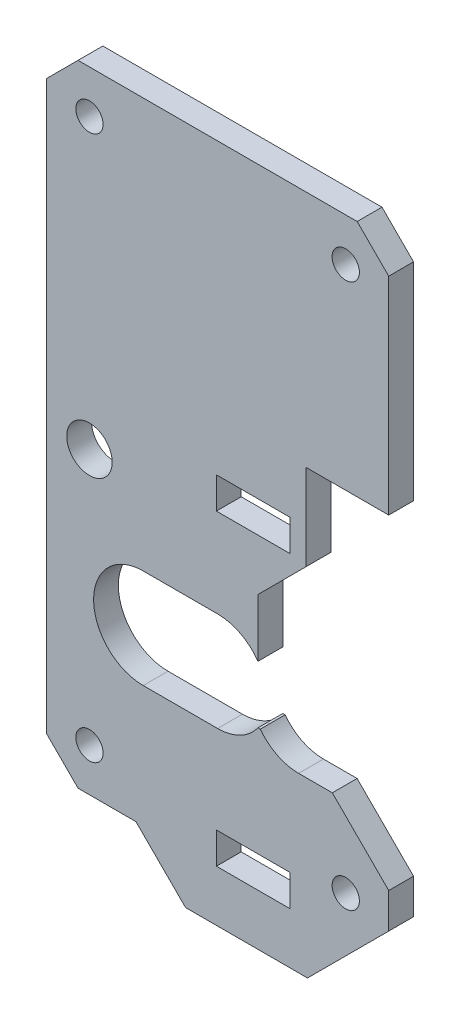
SolidWorks part; units mm, degrees
ref_plane "Front Plane" through (0, 0, 0) normal (0, 0, 1) x (1, 0, 0)
ref_plane "Top Plane" through (0, 0, 0) normal (0, 1, 0) x (1, 0, 0)
ref_plane "Right Plane" through (0, 0, 0) normal (1, 0, 0) x (0, 0, -1)
sketch "Sketch1" plane through (0, 0, 0) normal (0, 0, 1) x (1, 0, 0)
  line L0 (5.1665, -3.482) -> (4.8863, -3.482) construction
  line L1 (13.8757, -5.8) -> (9.805, -5.8) construction
  line L2 (20.7, 26.7) -> (20.7, 51.7327)
  line L3 (20.7, 26.7) -> (10.7, 26.7)
  line L4 (10.7, 26.7) -> (10.7, 16.2957)
  line L5 (10.7, 16.2957) -> (4.8863, 10.482)
  line L6 (4.8863, 10.482) -> (4.8863, 3.482)
  line L7 (20.7, -12.6243) -> (13.8757, -5.8) construction
  line L8 (20.7, -16.8757) -> (20.7, -12.6243) construction
  line L9 (10.8757, -26.7) -> (20.7, -16.8757) construction
  line L10 (2.5729, 20.5) -> (6.0371, 20.5)
  line L11 (2.5729, 55.55) -> (6.0371, 55.55)
  line L12 (2.5729, -20.5) -> (6.0371, -20.5)
  line L13 (6.0371, -26.7) -> (2.5729, -26.7)
  line L14 (5.1665, -3.482) -> (4.8863, -3.482)
  line L15 (13.8757, -5.8) -> (9.805, -5.8)
  line L16 (20.7, -12.6243) -> (13.8757, -5.8)
  line L17 (20.7, -16.8757) -> (20.7, -12.6243)
  line L18 (10.8757, -26.7) -> (20.7, -16.8757)
  line L84 (20.7, 51.7327) -> (16.8827, 55.55)
  line L85 (16.8827, 55.55) -> (6.0371, 55.55)
  line L87 (6.0371, 20.5) -> (8.755, 20.5)
  line L88 (8.755, 20.5) -> (8.755, 16.7)
  line L89 (8.755, 16.7) -> (-0.145, 16.7)
  line L90 (-0.145, 16.7) -> (-0.145, 20.5)
  line L91 (-0.145, 20.5) -> (2.5729, 20.5)
  line L93 (2.5729, 55.55) -> (-16.8827, 55.55)
  line L94 (-16.8827, 55.55) -> (-20.7, 51.7327)
  line L95 (-20.7, 51.7327) -> (-20.7, 16.8757)
  line L96 (-20.7, 16.8757) -> (-20.7, -16.8757)
  line L97 (-20.7, -16.8757) -> (-16.8757, -20.7)
  line L98 (-16.8757, -20.7) -> (-9.8757, -20.7)
  line L99 (-9.8757, -20.7) -> (-3.8757, -26.7)
  line L100 (-3.8757, -26.7) -> (2.5729, -26.7)
  line L102 (2.5729, -20.5) -> (-0.145, -20.5)
  line L103 (-0.145, -20.5) -> (-0.145, -16.7)
  line L104 (-0.145, -16.7) -> (8.755, -16.7)
  line L105 (8.755, -16.7) -> (8.755, -20.5)
  line L106 (8.755, -20.5) -> (6.0371, -20.5)
  line L108 (6.0371, -26.7) -> (10.8757, -26.7)
  line L114 (0, -6) -> (-9, -6)
  line L115 (-9, 6) -> (0, 6)
  line L120 (20.7, 18.1132) -> (12.7, 18.1132)
  arc A0 (5.1665, -3.482) -> (9.805, -5.8) centre (9.805, 0) ccw construction
  circle A1 centre (-15.5, -15.5) radius 1.65
  arc A2 (5.1665, -3.482) -> (9.805, -5.8) centre (9.805, 0) ccw
  circle A3 centre (15.5, -15.5) radius 1.65 construction
  arc A4 (0, -6) -> (4.8863, -3.482) centre (0, 0) ccw
  circle A5 centre (15.5, -15.5) radius 1.65
  arc A12 (-9, 6) -> (-9, -6) centre (-9, 0) ccw
  arc A13 (4.8863, 3.482) -> (0, 6) centre (0, 0) ccw
  circle A14 centre (-15.5, 15.5) radius 2.75
  circle A16 centre (-15.5, 50.35) radius 1.65
  circle A18 centre (15.5, 50.35) radius 1.65
  dimension "D7" = 3.3
  dimension "D1" = 5.5
  dimension "D8" = 3.3
  dimension "D9" = 3.3
  dimension "D10" = 6
  dimension "D11" = 6
  dimension "D12" = 6
  dimension "D2" = 135
  dimension "D3" = 10
  dimension "D4" = 7
  dimension "D13" = 2.5729
  dimension "D14" = 2.5729
  dimension "D16" = 4.8863
  dimension "D17" = 6.0371
  dimension "D18" = 6.0371
  dimension "D19" = 8.755
  dimension "D20" = 8.755
  dimension "D21" = 10.7
  dimension "D22" = 10.8757
  dimension "D23" = 12.7
  dimension "D24" = 15.5
  dimension "D25" = 16.8827
  dimension "D26" = 3.8757
  dimension "D27" = 9.8757
  dimension "D28" = 16.8757
  dimension "D29" = 16.8827
  dimension "D30" = 3.482
  dimension "D31" = 0.145
  dimension "D32" = 0.145
  dimension "D33" = 15.5
  dimension "D34" = 16.8757
  dimension "D35" = 9
  dimension "D36" = 9
  dimension "D37" = 26.7
  dimension "D38" = 3.482
  dimension "D39" = 15.5
  dimension "D40" = 15.5
  dimension "D41" = 15.5
  dimension "D42" = 16.7
  dimension "D43" = 16.7
  dimension "D44" = 16.8757
  dimension "D45" = 20.7
  dimension "D46" = 20.7
  dimension "D47" = 26.7
  dimension "D48" = 18.1132
  dimension "D49" = 18.1132
  dimension "D50" = 20.5
  dimension "D51" = 20.5
  dimension "D54" = 50.35
  dimension "D55" = 50.35
  dimension "D56" = 51.7327
  dimension "D57" = 51.7327
  dimension "D58" = 55.55
  dimension "D59" = 55.55
  dimension "D66" = 16.7
  dimension "D67" = 16.7
  dimension "D70" = 20.5
  dimension "D71" = 20.5
  dimension "D72" = 20.7
  dimension "D73" = 20.7
  dimension "D74" = 26.7
extrude "Boss-Extrude1" add sketch "Sketch1" along normal blind 3
